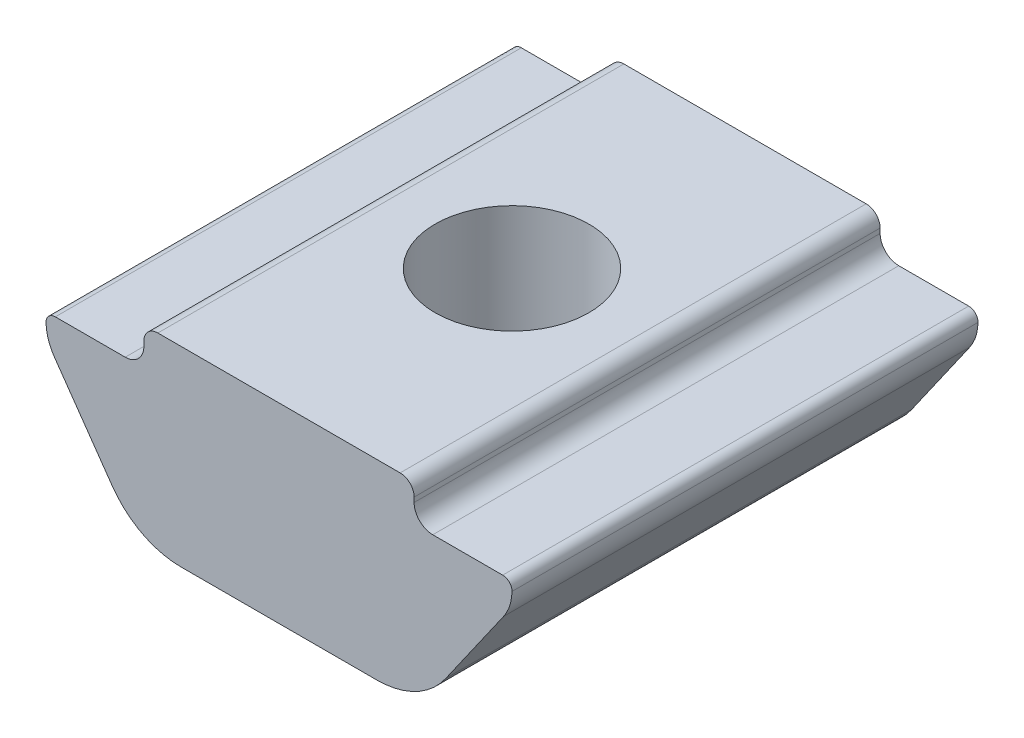
SolidWorks part; units mm, degrees
ref_plane "正面" through (0, 0, 0) normal (0, 0, 1) x (1, 0, 0)
ref_plane "平面" through (0, 0, 0) normal (0, 1, 0) x (1, 0, 0)
ref_plane "右側面" through (0, 0, 0) normal (1, 0, 0) x (0, 0, -1)
sketch "レイアウトスケッチ" plane through (0, 0, 0) normal (0, 0, 1) x (0, 1, 0)
  line L0 (-1.5582, -4.8192) -> (-3.3322, -3.5774)
  line L1 (0.45, 0) -> (-4.55, 0) construction
  line L2 (-0.3, 2.9) -> (-0.4, 2.9)
  line L3 (-0.3, -2.9) -> (-0.4, -2.9)
  line L4 (0.95, 0) -> (-5.05, 0) construction
  line L5 (-0.8, 4.8) -> (-0.8, 3.3)
  line L6 (-0.8, -4.8) -> (-0.8, -3.3)
  line L7 (-0.8, -4.8) -> (-0.8, -3.3)
  line L8 (-1.5582, 4.8192) -> (-3.3322, 3.5774)
  line L9 (-0.8, 4.8) -> (-0.8, 3.3)
  line L10 (0, 2.6) -> (0, 0)
  line L11 (-0.3, 2.9) -> (-0.4, 2.9)
  line L12 (-0.3, -2.9) -> (-0.4, -2.9)
  line L13 (0, -2.6) -> (0, 0)
  line L14 (-4.1, 2.1028) -> (-4.1, -2.1028)
  line L15 (14.25, 5) -> (24.25, 5)
  line L16 (14.25, -5) -> (24.25, -5)
  line L17 (14.25, 5) -> (14.25, -5)
  line L18 (24.25, 5) -> (24.25, -5)
  line L19 (14.25, 2.9) -> (24.25, 2.9)
  line L20 (14.25, -2.9) -> (24.25, -2.9)
  line L21 (-4.1, 14.7667) -> (0, 14.7667)
  line L22 (-4.1, 24.7667) -> (0, 24.7667)
  line L23 (0, 24.7667) -> (0, 14.7667)
  line L24 (-4.1, 24.7667) -> (-4.1, 14.7667)
  line L25 (-0.8, 24.7667) -> (-0.8, 14.7667)
  line L26 (-5.05, 19.7667) -> (0.95, 19.7667) construction
  line L27 (19.25, 4) -> (19.25, -4) construction
  line L28 (15.25, 0) -> (23.25, 0) construction
  line L29 (-4.1, 1.5) -> (0, 1.5) construction
  line L30 (-4.1, 1.2295) -> (0, 1.2295) construction
  line L31 (-4.1, -1.2295) -> (0, -1.2295) construction
  line L32 (-4.1, -1.5) -> (0, -1.5) construction
  line L33 (-4.1, 21.2667) -> (0, 21.2667) construction
  line L34 (-4.1, 20.9962) -> (0, 20.9962) construction
  line L35 (-4.1, 18.5372) -> (0, 18.5372) construction
  line L36 (-4.1, 18.2667) -> (0, 18.2667) construction
  line L37 (-1.3, 24.7667) -> (-1.3, 14.7667)
  arc A0 (-1.5582, -4.8192) -> (-1.0123, -4.9996) centre (-0.9848, -4) ccw
  arc A1 (-4.1, -2.1028) -> (-3.3322, -3.5774) centre (-2.3, -2.1028) ccw
  arc A2 (-0.3, -2.9) -> (0, -2.6) centre (-0.3, -2.6) ccw
  arc A3 (-1.0123, -4.9996) -> (-0.8, -4.8) centre (-1, -4.8) ccw
  arc A4 (-0.8, 4.8) -> (-1.0123, 4.9996) centre (-1, 4.8) ccw
  arc A5 (-0.4, -2.9) -> (-0.8, -3.3) centre (-0.4, -3.3) ccw
  arc A6 (0, 2.6) -> (-0.3, 2.9) centre (-0.3, 2.6) ccw
  arc A7 (-3.3322, 3.5774) -> (-4.1, 2.1028) centre (-2.3, 2.1028) ccw
  arc A8 (-1.0123, 4.9996) -> (-1.5582, 4.8192) centre (-0.9848, 4) ccw
  arc A9 (-0.8, 3.3) -> (-0.4, 2.9) centre (-0.4, 3.3) ccw
  circle A10 centre (19.25, 0) radius 1.5
  circle A11 centre (19.25, 0) radius 1.2295
sketch "ｽｹｯﾁ2" plane through (0, 0, 0) normal (0, 0, 1) x (1, 0, 0)
  line L0 (2.8999, -0.3) -> (2.8999, -0.4)
  line L1 (4.7999, -0.8) -> (3.2999, -0.8)
  line L2 (4.8192, -1.5582) -> (3.5774, -3.3322)
  line L5 (-2.1028, -4.1) -> (2.1028, -4.1)
  line L6 (-4.8192, -1.5582) -> (-3.5774, -3.3322)
  line L7 (-4.7999, -0.8) -> (-3.2999, -0.8)
  line L8 (-2.8999, -0.3) -> (-2.8999, -0.4)
  line L9 (-2.5999, 0) -> (2.5999, 0)
  line L10 (0, 0) -> (0, -4.1) construction
  arc A0 (2.5999, 0) -> (2.8999, -0.3) centre (2.5999, -0.3) cw
  arc A1 (3.2999, -0.8) -> (2.8999, -0.4) centre (3.2999, -0.4) cw
  arc A2 (4.7999, -0.8) -> (4.9998, -1.0038) centre (4.7999, -1) cw
  arc A3 (4.9998, -1.0038) -> (4.8192, -1.5582) centre (4, -0.9848) cw
  arc A4 (3.5774, -3.3322) -> (2.1028, -4.1) centre (2.1028, -2.3) cw
  arc A5 (-3.5774, -3.3322) -> (-2.1028, -4.1) centre (-2.1028, -2.3) ccw
  arc A6 (-4.9998, -1.0038) -> (-4.8192, -1.5582) centre (-4, -0.9848) ccw
  arc A7 (-4.7999, -0.8) -> (-4.9998, -1.0038) centre (-4.7999, -1) ccw
  arc A8 (-3.2999, -0.8) -> (-2.8999, -0.4) centre (-3.2999, -0.4) ccw
  arc A9 (-2.5999, 0) -> (-2.8999, -0.3) centre (-2.5999, -0.3) ccw
  dimension "D3" = 0.3
  dimension "D4" = 1.8
  dimension "D6" = 0.4
  dimension "D7" = 0.2
  dimension "D11" = 1
  dimension "D1" = 4.1
  dimension "D5" = 5.7997
  dimension "D8" = 0.8
  dimension "D9" = 9.9996
  dimension "D10" = 124.992
  dimension "D12" = 2.1654
  dimension "D13" = 1.5
extrude "押し出し1" add sketch "ｽｹｯﾁ2" along normal mid plane 10
hole_wizard "M4x0.7 ねじ穴1" positions "ｽｹｯﾁ6" profile "ｽｹｯﾁ5" tap size "M4x0.7" standard "JIS" end condition through all
sketch "ｽｹｯﾁ6" plane through (0, 0, 0) normal (0, 1, 0) x (-1, 0, 0)
  point P0 (0, 0)
cosmetic thread "ねじ山1" parameters "D2"=4
sketch "ｽｹｯﾁ5" plane through (0, 0, 0) normal (1, 0, 0) x (0, 0, 1)
  line L0 (0, 0) -> (0, 4.1)
  line L1 (0, 4.1) -> (1.65, 4.1)
  line L2 (1.65, 4.1) -> (1.65, 0)
  line L5 (1.65, 0) -> (0, 0)
  line L11 (0, -6.35) -> (0, 107.95) construction
  dimension "次ｻｰﾌｪｽまでのねじ下穴ﾄﾞﾘﾙの直径" = 3.3
  dimension "次ｻｰﾌｪｽまでのねじ下穴ﾄﾞﾘﾙの深さ" = 4.1
